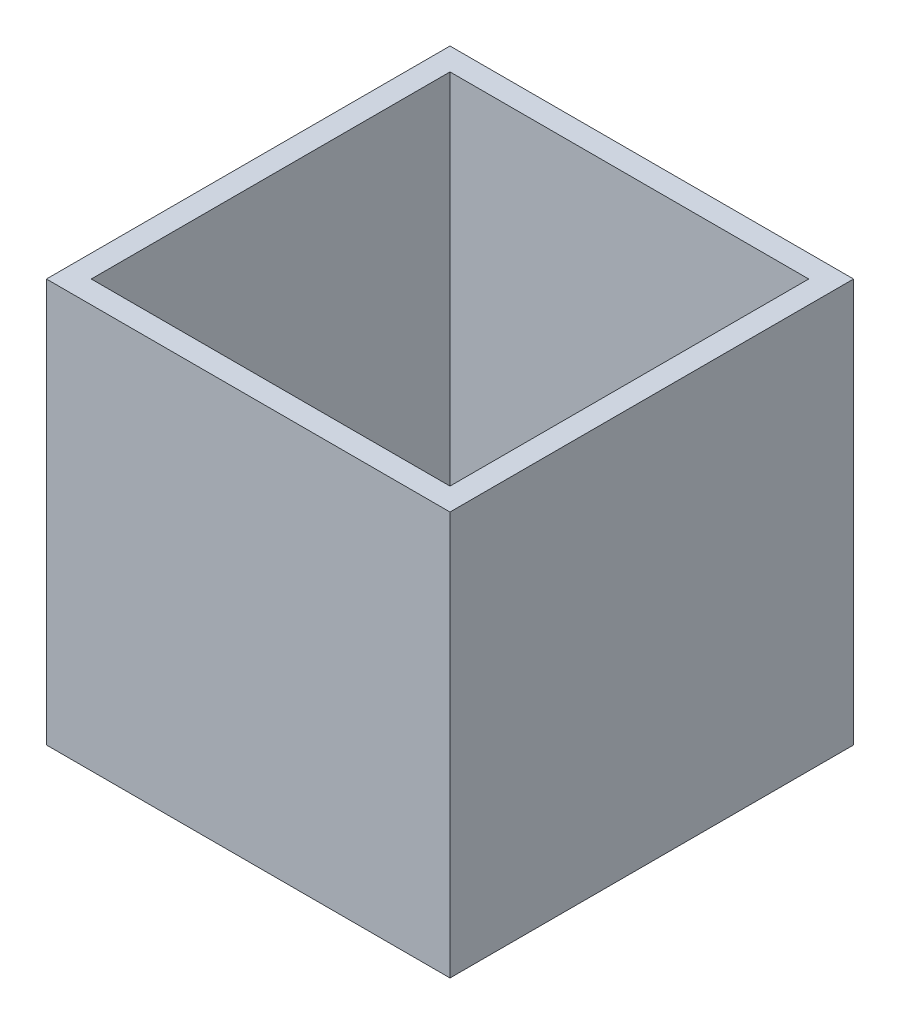
SolidWorks part; units mm, degrees
ref_plane "Front Plane" through (0, 0, 0) normal (0, 0, 1) x (1, 0, 0)
ref_plane "Top Plane" through (0, 0, 0) normal (0, 1, 0) x (1, 0, 0)
ref_plane "Right Plane" through (0, 0, 0) normal (1, 0, 0) x (0, 0, -1)
sketch "Sketch1" plane through (0, 0, 0) normal (0, 1, 0) x (1, 0, 0)
  line L1 (9, 9) -> (-9, 9)
  line L2 (9, 9) -> (9, -9)
  line L3 (9, -9) -> (-9, -9)
  line L4 (-9, 9) -> (-9, -9)
  line L5 (9, 9) -> (-9, -9) construction
  line L6 (9, -9) -> (-9, 9) construction
  point P0 (0, 0)
  dimension "D1" = 18
extrude "Boss-Extrude1" add sketch "Sketch1" along normal blind 18
shell "Shell1" thickness 1
equation "\"L\"= 18'length of a rib"
equation "\"D1@Sketch1\"=\"L\""
equation "\"D1@Boss-Extrude1\"=\"L\""
